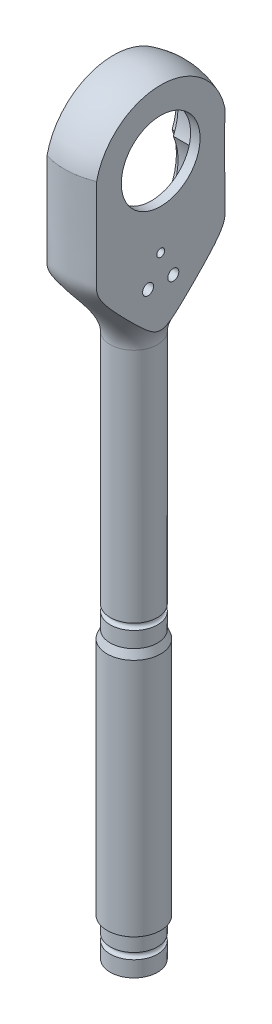
SolidWorks part; units mm, degrees
ref_plane "Front Plane" through (0, 0, 0) normal (0, 0, 1) x (1, 0, 0)
ref_plane "Top Plane" through (0, 0, 0) normal (0, 1, 0) x (1, 0, 0)
ref_plane "Right Plane" through (0, 0, 0) normal (1, 0, 0) x (0, 0, -1)
sketch "Szkic1" plane through (0, 0, 0) normal (0, 0, 1) x (1, 0, 0)
  line L0 (0, 0) -> (7.5, 0)
  line L1 (7.5, 0) -> (7.5, 5)
  line L2 (7.5, 7) -> (7.5, 11.25)
  line L3 (8.25, 12) -> (8.5, 12)
  line L4 (8.5, 12) -> (8.5, 88)
  line L5 (8.5, 88) -> (7.5, 90.5)
  line L6 (7.5, 90.5) -> (7.5, 95.5)
  line L7 (7.5, 97.5) -> (7.5, 172.5)
  line L8 (0, 0) -> (0, 246)
  line L9 (22.0454, 242.9689) -> (22.0454, 213.0311) construction
  line L10 (7.5, 176.4545) -> (7.5, 154.3641) construction
  arc A0 (7.5, 5) -> (7.5, 7) centre (7.5, 6) cw
  arc A1 (7.5, 95.5) -> (7.5, 97.5) centre (7.5, 96.5) cw
  arc A2 (0, 246) -> (22.0454, 228) centre (0, 223.5) cw
  arc A3 (7.5, 11.25) -> (8.25, 12) centre (8.25, 11.25) cw
  spline S0 degree 3 poles (7.5, 172.5) (7.5, 180.6) (22.3824, 192.8322) (21.8956, 206.4841) (22.0454, 220.5) (22.0454, 228) knots 0 0 0 0 0.361711 0.461711 1 1 1 1
  point P40 (7.5, 12)
  dimension "D4" = 1
  dimension "D8" = 1
  dimension "D13" = 22.5
  dimension "D14" = 30
  dimension "D15" = 25
  dimension "D16" = 45
  dimension "D17" = 27
  dimension "D18" = 0.75
  dimension "D1" = 7.5
  dimension "D2" = 5
  dimension "D3" = 5
  dimension "D5" = 8.5
  dimension "D6" = 76
  dimension "D7" = 2.5
  dimension "D9" = 5
  dimension "D10" = 75
  dimension "D11" = 246
  dimension "D12" = 18
revolve "Obrót1" add sketch "Szkic1" angle 360 about L8
sketch "Szkic2" plane through (0, 0, 0) normal (0, 0, 1) x (1, 0, 0)
  line L0 (-7.5, 168) -> (-6.5, 173)
  line L1 (-7.5, 172.5) -> (-7.5, 97.5) construction
  line L2 (-6.5, 173) -> (-6.5, 255.3212)
  line L3 (-6.5, 255.3212) -> (-63.3244, 255.3212)
  line L4 (-63.3244, 255.3212) -> (-63.3244, 168)
  line L5 (-63.3244, 168) -> (-7.5, 168)
  line L6 (-7.5, 0) -> (7.5, 0) construction
  line L8 (8.5, 168) -> (39.7906, 168)
  line L9 (8.5, 168) -> (8.5, 255.3212)
  line L10 (8.5, 255.3212) -> (39.7906, 255.3212)
  line L11 (39.7906, 168) -> (39.7906, 255.3212)
  dimension "D1" = 168
  dimension "D2" = 5
  dimension "D3" = 1
  dimension "D4" = 15
extrude "Wytnij-wyciągnięcie1" cut sketch "Szkic2" against normal through all both and the other way through all
sketch "Szkic3" plane through (-6.5, 0, 0) normal (-1, 0, 0) x (0, 0, 1)
  arc A0 (18.6397, 215.25) -> (-18.6397, 215.25) centre (0, 222.5) ccw
  arc A1 (-18.6397, 215.25) -> (18.6397, 215.25) centre (0, 208) ccw
  dimension "D1" = 40
  dimension "D3" = 14.5
  dimension "D4" = 40
  dimension "D2" = 222.5
extrude "Wytnij-wyciągnięcie2" cut sketch "Szkic3" against normal blind 2
sketch "Szkic4" plane through (-6.5, 0, 0) normal (-1, 0, 0) x (0, 0, 1)
  arc A5 (-17.0202, 215.25) -> (17.0202, 215.25) centre (0, 208) ccw
  arc A6 (17.0202, 215.25) -> (-17.0202, 215.25) centre (0, 222.5) ccw
  arc A7 (-17.0202, 215.25) -> (17.0202, 215.25) centre (0, 208) ccw
  arc A8 (17.0202, 215.25) -> (-17.0202, 215.25) centre (0, 222.5) ccw
  dimension "D1" = 1.5
extrude "Wytnij-wyciągnięcie3" cut sketch "Szkic4" against normal blind 12
sketch "Szkic5" plane through (5.5, 0, 0) normal (-1, 0, 0) x (0, 0, 1)
  line L0 (0, 0) -> (0, 253.867) construction
  circle A0 centre (4, 190.1938) radius 1.75
  arc A3 (-18.6397, 215.25) -> (18.6397, 215.25) centre (0, 208) ccw construction
  circle A4 centre (-4, 190.1938) radius 1.75
  circle A5 centre (0, 198.256) radius 1.25
  circle A6 centre (0, 223.5) radius 12.5
  arc A7 (21.0654, 228) -> (-21.0654, 228) centre (0, 223.5) ccw construction
  dimension "D1" = 3.5
  dimension "D3" = 2.5
  dimension "D5" = 25
  dimension "D2" = 4
  dimension "D4" = 9
extrude "Wytnij-wyciągnięcie4" cut sketch "Szkic5" against normal through all both and the other way through all
sketch "Szkic7" plane through (0, 0, 0) normal (1, 0, 0) x (0, 0, -1)
  arc A0 (-17.0202, 215.25) -> (17.0202, 215.25) centre (0, 208) ccw construction
  point P0 (-16.6808, 200)
  point P1 (16.6808, 200)
  point P5 (0, 0)
  dimension "D1" = 200
